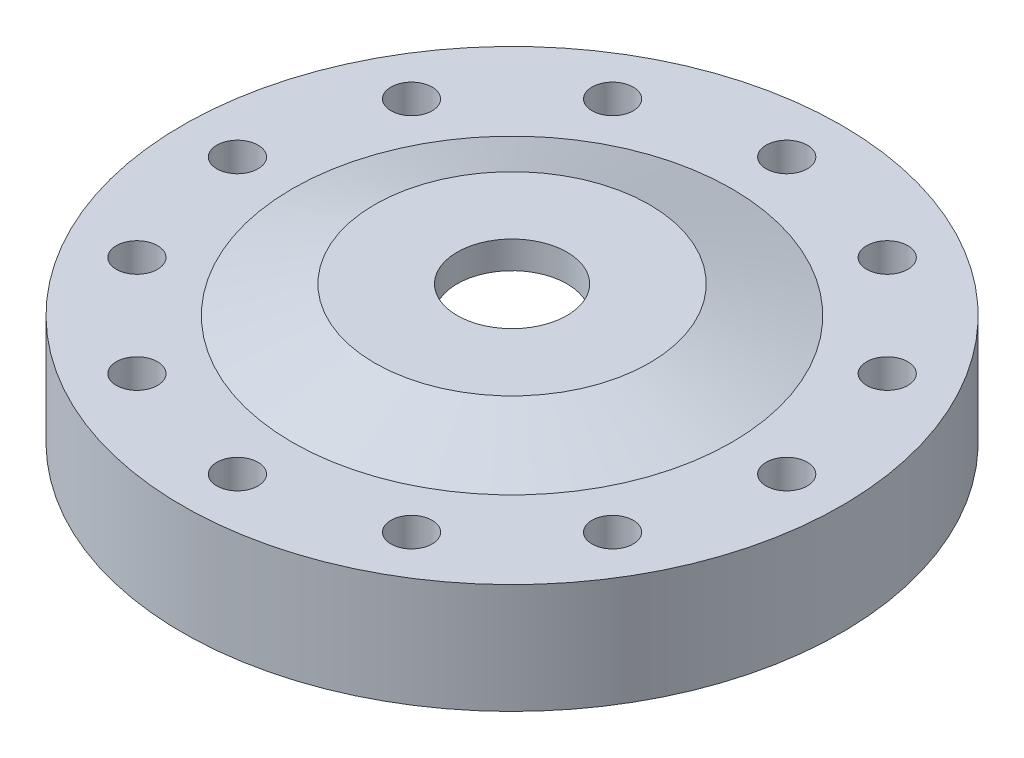
SolidWorks part; units mm, degrees
ref_plane "Front Plane" through (0, 0, 0) normal (0, 0, 1) x (1, 0, 0)
ref_plane "Top Plane" through (0, 0, 0) normal (0, 1, 0) x (1, 0, 0)
ref_plane "Right Plane" through (0, 0, 0) normal (1, 0, 0) x (0, 0, -1)
ref_axis "Axis1" through (0, -1.5875, 0) along (0, 1, 0)
sketch "Sketch1" plane through (0, 0, 0) normal (0, 0, 1) x (1, 0, 0)
  line L0 (-76.2, 0) -> (-76.2, 25.4)
  line L1 (-76.2, 25.4) -> (-50.8, 25.4)
  line L2 (-50.8, 25.4) -> (-31.75, 31.75)
  line L3 (-31.75, 31.75) -> (-12.7, 31.75)
  line L4 (-12.7, 31.75) -> (-12.7, 25.4)
  line L6 (-31.75, 15.875) -> (-31.75, 12.7)
  line L7 (-36.0807, 12.7) -> (-50.8, 12.7)
  line L8 (-50.8, 12.7) -> (-50.8, 0)
  line L9 (-55.1307, 0) -> (-76.2, 0)
  line L10 (-36.0807, 12.7) -> (-36.0807, 14.732)
  line L11 (-36.0807, 14.732) -> (-33.3375, 14.732)
  line L12 (-33.3375, 14.732) -> (-33.3375, 12.7)
  line L13 (-33.3375, 12.7) -> (-31.75, 12.7)
  line L14 (-31.75, 15.875) -> (-12.7, 25.4)
  line L15 (-50.8, 0) -> (-52.3875, 0)
  line L16 (-52.3875, 0) -> (-52.3875, 2.032)
  line L17 (-52.3875, 2.032) -> (-55.1307, 2.032)
  line L18 (-55.1307, 2.032) -> (-55.1307, 0)
  point P18 (-55.7704, 0)
  dimension "D1" = 25.4
  dimension "D2" = 76.2
  dimension "D3" = 12.7
  dimension "D4" = 12.7
  dimension "D5" = 2.7432
  dimension "D6" = 2.032
  dimension "D7" = 1.5875
  dimension "D8" = 31.75
  dimension "D9" = 19.05
  dimension "D10" = 6.35
  dimension "D11" = 3.175
  dimension "D12" = 31.75
  dimension "D13" = 25.4
  dimension "D14" = 19.05
  dimension "D15" = 2.7432
  dimension "D16" = 2.032
  dimension "D17" = 1.5875
revolve "Revolve1" add sketch "Sketch1" angle 360 about axis through (0, -1.5875, 0) along (0, 1, 0)
hole_wizard "3/8 (0.375) Diameter Hole1" positions "Sketch2" profile "Sketch3" hole size "3/8" standard "ANSI Inch"
sketch "Sketch2" plane through (0, 25.4, 0) normal (0, 1, 0) x (1, 0, 0)
  point P0 (-63.5, 0)
  dimension "D1" = 63.5
sketch "Sketch3" plane through (-63.5, 25.4, 0) normal (1, 0, 0) x (0, 0, 1)
  line L0 (0, 0) -> (0, 53.6616)
  line L1 (0, 53.6616) -> (4.7625, 50.8)
  line L2 (4.7625, 50.8) -> (4.7625, 0)
  line L5 (4.7625, 0) -> (0, 0)
  line L10 (0, 53.6616) -> (-4.7625, 50.8) construction
  line L11 (0, -6.35) -> (0, 107.95) construction
  dimension "Hole Dia." = 9.525
  dimension "Hole Depth" = 50.8
  dimension "Drill Angle" = 118
pattern_circular "CirPattern1" count 12 over 360 about axis through (0, 0, 0) along (0, 1, 0) of "3/8 (0.375) Diameter Hole1"
